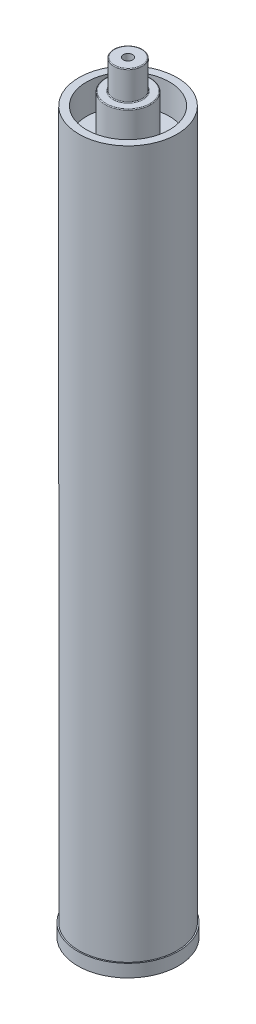
SolidWorks part; units mm, degrees
ref_plane "Front Plane" through (0, 0, 0) normal (0, 0, 1) x (1, 0, 0)
ref_plane "Top Plane" through (0, 0, 0) normal (0, 1, 0) x (1, 0, 0)
ref_plane "Right Plane" through (0, 0, 0) normal (1, 0, 0) x (0, 0, -1)
sketch "Sketch1" plane through (0, 0, 0) normal (0, 1, 0) x (1, 0, 0)
  circle A0 centre (0, 0) radius 14.351
  dimension "D1" = 28.702
extrude "Boss-Extrude1" add sketch "Sketch1" against normal blind 29.2608
sketch "Sketch2" plane through (0, -29.2608, 0) normal (0, -1, 0) x (1, 0, 0)
  circle A0 centre (0, 0) radius 22.6949
  dimension "D1" = 45.3898
extrude "Boss-Extrude2" add sketch "Sketch2" along normal blind 42.9006
sketch "Sketch3" plane through (0, -72.1614, 0) normal (0, -1, 0) x (1, 0, 0)
  circle A0 centre (0, 0) radius 49.2379
  dimension "D1" = 98.4758
extrude "Boss-Extrude3" add sketch "Sketch3" along normal blind 679.704
sketch "Sketch4" plane through (0, -72.1614, 0) normal (0, 1, 0) x (1, 0, 0)
  circle A0 centre (0, 0) radius 49.2379 construction
  circle A1 centre (0, 0) radius 49.2379
  circle A2 centre (0, 0) radius 41.6179
  dimension "D1" = 83.2358
extrude "Boss-Extrude4" add sketch "Sketch4" along normal blind 29.9212
sketch "Sketch5" plane through (0, 0, 0) normal (0, 1, 0) x (1, 0, 0)
  circle A0 centre (0, 0) radius 4.6418
  dimension "D1" = 9.2837
extrude "Cut-Extrude1" cut sketch "Sketch5" against normal blind 74.9986
sketch "Sketch6" plane through (0, -751.8654, 0) normal (0, -1, 0) x (1, 0, 0)
  circle A0 centre (0, 0) radius 50.5079
  dimension "D1" = 101.0158
extrude "Boss-Extrude5" add sketch "Sketch6" along normal blind 12.7
ref_plane "Plane1" through (0, -747.8374, 0) normal (0, -1, 0) x (-1, 0, 0)
sketch "Sketch8" plane through (0, -764.5654, 0) normal (0, -1, 0) x (1, 0, 0)
  circle A0 centre (0, 0) radius 44.6213
  dimension "D1" = 89.2426
sketch "Sketch9" plane through (0, -747.8374, 0) normal (0, -1, 0) x (-1, 0, 0)
  circle A0 centre (0, 0) radius 38.9
  dimension "D1" = 77.8
loft "Cut-Loft1" cut profiles "Sketch9", "Sketch8"
fillet "Fillet1" radius 0.762 4 edges at (0, -72.1614, -22.6949) (0, -29.2608, 14.351) (0, -29.2608, -22.6949) (0, 0, 14.351)
